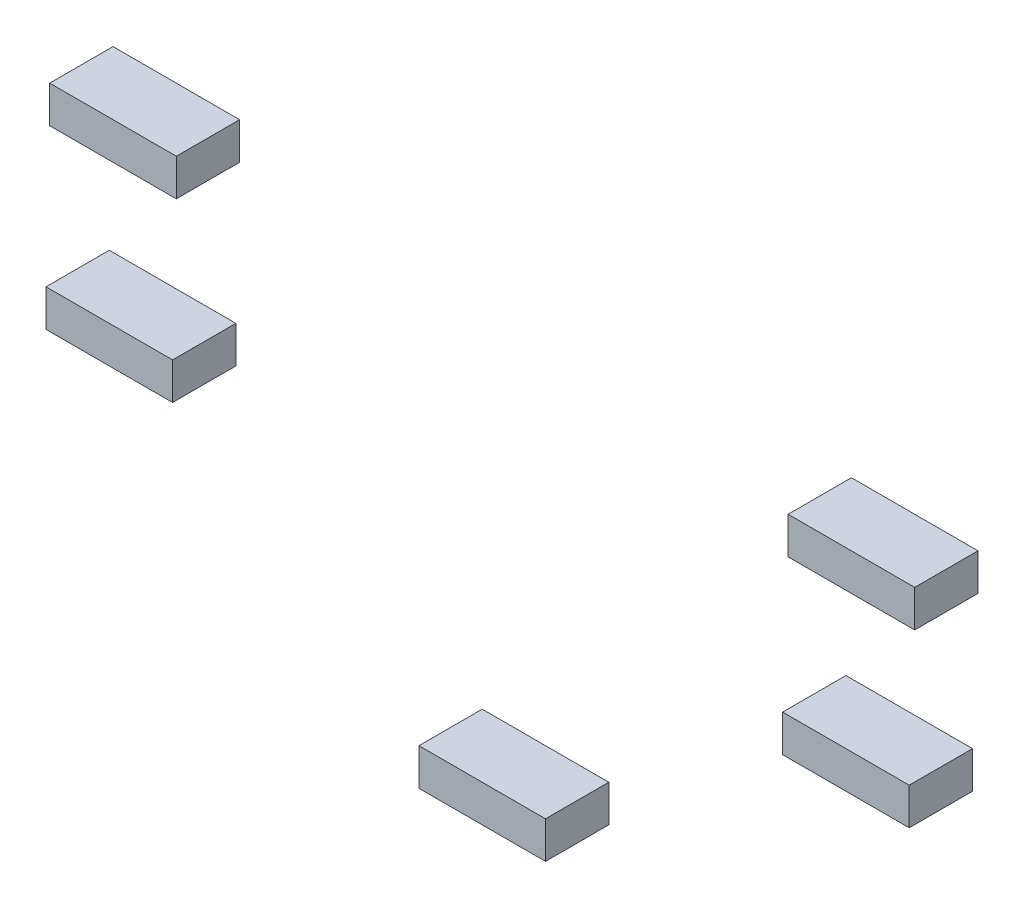
SolidWorks part; units mm, degrees
ref_plane "Front Plane" through (0, 0, 0) normal (0, 0, 1) x (1, 0, 0)
ref_plane "Top Plane" through (0, 0, 0) normal (0, 1, 0) x (1, 0, 0)
ref_plane "Right Plane" through (0, 0, 0) normal (1, 0, 0) x (0, 0, -1)
sketch "Sketch1" plane through (0, 0, 0) normal (0, 0, 1) x (1, 0, 0)
  line L0 (67537.0577, 23695.7019) -> (67537.0577, 23591.6336) construction
  line L1 (66337.0577, 23766.6336) -> (67537.0577, 23766.6336)
  line L2 (66337.0577, 23766.6336) -> (66337.0577, 23416.6336)
  line L3 (66337.0577, 23416.6336) -> (67537.0577, 23416.6336)
  line L4 (67537.0577, 23766.6336) -> (67537.0577, 23416.6336)
  line L5 (69785.1426, 25766.6336) -> (70985.1426, 25766.6336)
  line L6 (69785.1426, 25766.6336) -> (69785.1426, 25416.6336)
  line L7 (69785.1426, 25416.6336) -> (70985.1426, 25416.6336)
  line L8 (70985.1426, 25766.6336) -> (70985.1426, 25416.6336)
  line L9 (71037.0577, 27066.6336) -> (69837.0577, 27066.6336)
  line L10 (71037.0577, 27066.6336) -> (71037.0577, 27416.6336)
  line L11 (71037.0577, 27416.6336) -> (69837.0577, 27416.6336)
  line L12 (69837.0577, 27066.6336) -> (69837.0577, 27416.6336)
  line L13 (64037.0577, 27106.1704) -> (62837.0577, 27106.1704)
  line L14 (64037.0577, 27106.1704) -> (64037.0577, 27456.1704)
  line L15 (64037.0577, 27456.1704) -> (62837.0577, 27456.1704)
  line L16 (62837.0577, 27106.1704) -> (62837.0577, 27456.1704)
  line L17 (62801.8192, 25766.4437) -> (64001.8192, 25766.4437)
  line L18 (62801.8192, 25766.4437) -> (62801.8192, 25416.4437)
  line L19 (62801.8192, 25416.4437) -> (64001.8192, 25416.4437)
  line L20 (64001.8192, 25766.4437) -> (64001.8192, 25416.4437)
  line L21 (67537.0577, 23591.6336) -> (66337.0577, 23591.6336) construction
  line L22 (70985.1426, 25591.6336) -> (69785.1426, 25591.6336) construction
  line L23 (71037.0577, 27241.6336) -> (69837.0577, 27241.6336) construction
  line L24 (62837.0577, 27281.1704) -> (64037.0577, 27281.1704) construction
  line L25 (62801.8192, 25591.4437) -> (64001.8192, 25591.4437) construction
  line L26 (70437.0577, 27416.6336) -> (70437.0577, 25073.218) construction
  line L27 (63437.0577, 27456.1704) -> (63437.0577, 25416.4437) construction
  line L28 (66937.0577, 23766.6336) -> (66937.0577, 23416.6336) construction
  line L29 (71187.0577, 22391.6336) -> (66451.8142, 22391.6336) construction
  line L30 (70437.0577, 28624.2311) -> (70437.0577, 24879.1336) construction
  line L31 (70132.2577, 28624.2311) -> (70741.8577, 28624.2311) construction
  dimension "D1" = 7000
  dimension "D2" = 3500
  dimension "D3" = 1200
  dimension "D4" = 1200
  dimension "D5" = 1200
  dimension "D6" = 1200
  dimension "D7" = 350
  dimension "D8" = 350
  dimension "D9" = 350
  dimension "D10" = 350
  dimension "D11" = 350
  dimension "D12" = 1200
  dimension "D13" = 3500
  dimension "D14" = 3200
  dimension "D15" = 4850
  dimension "D16" = 1200
extrude "Extrude1" add sketch "Sketch1" along normal blind 600
ref_plane "Plane1" through (66937.0577, 0, 0) normal (-1, 0, 0) x (0, 0, 1)
